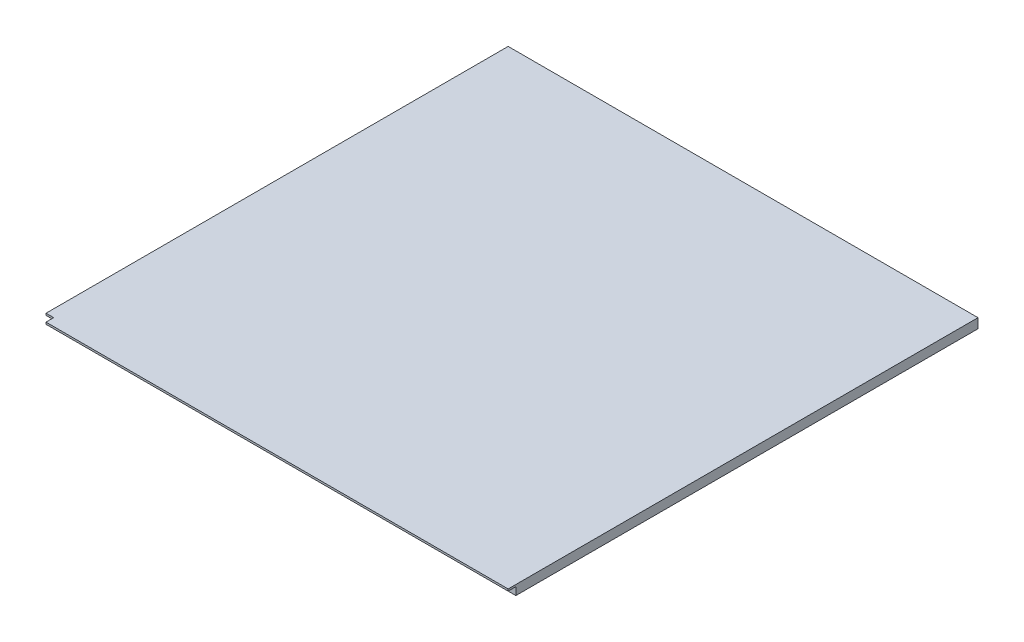
SolidWorks part; units mm, degrees
ref_plane "Front Plane" through (0, 0, 0) normal (0, 0, 1) x (1, 0, 0)
ref_plane "Top Plane" through (0, 0, 0) normal (0, 1, 0) x (1, 0, 0)
ref_plane "Right Plane" through (0, 0, 0) normal (1, 0, 0) x (0, 0, -1)
sketch "Sketch1" plane through (0, 0, 0) normal (0, 1, 0) x (1, 0, 0)
  line L1 (0, 0) -> (152.4, 0)
  line L2 (0, 0) -> (0, 152.4)
  line L3 (0, 152.4) -> (152.4, 152.4)
  line L4 (152.4, 0) -> (152.4, 152.4)
  dimension "D1" = 152.4
  dimension "D2" = 152.4
extrude "Boss-Extrude1" add sketch "Sketch1" along normal blind 3.175
sketch "Sketch2" plane through (0, 3.175, 0) normal (0, 1, 0) x (1, 0, 0)
  line L8 (0, 152.4) -> (-2.54, 152.4)
  line L9 (-2.54, 152.4) -> (-2.54, -2.54)
  line L10 (-2.54, -2.54) -> (152.4, -2.54)
  line L11 (152.4, -2.54) -> (152.4, 0)
  line L13 (152.4, 0) -> (152.4, 152.4) construction
  line L14 (0, 0) -> (152.4, 0) construction
  line L15 (152.4, 0) -> (0, 0)
  line L16 (0, 0) -> (0, 152.4)
  dimension "D1" = 2.54
  dimension "D2" = 2.54
extrude "Boss-Extrude2" add sketch "Sketch2" against normal blind 0.635
sketch "Sketch3" plane through (0, 3.175, 0) normal (0, 1, 0) x (1, 0, 0)
  line L1 (-2.54, -2.54) -> (0, -2.54)
  line L2 (-2.54, -2.54) -> (-2.54, 0)
  line L3 (-2.54, 0) -> (0, 0)
  line L4 (0, -2.54) -> (0, 0)
extrude "Cut-Extrude1" cut sketch "Sketch3" against normal through all
